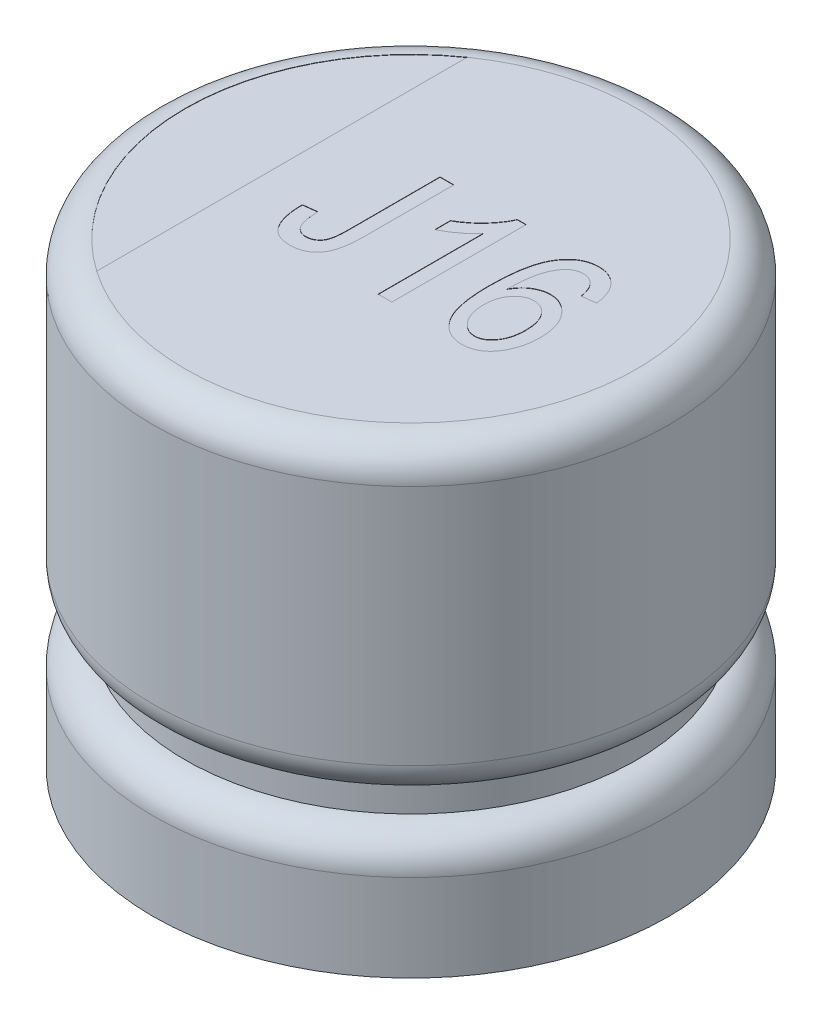
SolidWorks part; units mm, degrees
material "1060-H16"
ref_plane "Front Plane" through (0, 0, 0) normal (0, 0, 1) x (1, 0, 0)
ref_plane "Top Plane" through (0, 0, 0) normal (0, 1, 0) x (1, 0, 0)
ref_plane "Right Plane" through (0, 0, 0) normal (1, 0, 0) x (0, 0, -1)
sketch "Sketch1" plane through (0, 0, 0) normal (0, 1, 0) x (1, 0, 0)
  circle A0 centre (0, 0) radius 8
  dimension "D1" = 16
extrude "Boss-Extrude1" add sketch "Sketch1" along normal blind 14.2
fillet "Fillet1" radius 1 1 edges at (0, 14.2, 8)
sketch "Sketch2" plane through (0, 0, 0) normal (0, 0, 1) x (1, 0, 0)
  line L0 (-8, 13.2) -> (-8, 0) construction
  line L1 (-8, 5.7) -> (-7, 5.7) construction
  line L2 (-8, 5.7) -> (-8, 2.7)
  line L3 (-8, 2.7) -> (-7, 2.7) construction
  line L4 (-7, 5.7) -> (-7, 2.7) construction
  line L5 (7, 14.2) -> (-7, 14.2) construction
  line L6 (-7, 4.7) -> (-7, 3.7)
  arc A0 (-8, 5.7) -> (-7, 4.7) centre (-7, 5.7) ccw
  arc A1 (-7, 3.7) -> (-8, 2.7) centre (-7, 2.7) ccw
  point P8 (-8, 4.2)
  dimension "D1" = 1
  dimension "D2" = 10
  dimension "D3" = 3
ref_axis "Axis1" through (0, -0.75, 0) along (0, 1, 0)
revolve "Cut-Revolve1" cut sketch "Sketch2" angle 360 about axis through (0, -0.75, 0) along (0, 1, 0)
sketch "Sketch3" plane through (0, 14.2, 0) normal (0, 1, 0) x (1, 0, 0)
  line L0 (-4, 5.7446) -> (-4, -5.7446)
  line L1 (0, -55) -> (0, 55) construction
  arc A0 (-4, 5.7446) -> (-4, -5.7446) centre (0, 0) ccw
  circle A1 centre (0, 0) radius 7 construction
  dimension "D1" = 4
extrude "Cut-Extrude1" cut sketch "Sketch3" against normal blind 0.01
sketch "Sketch4" plane through (0, 14.2, 0) normal (0, 1, 0) x (1, 0, 0)
  line L0 (-2.7025, -2) -> (2.7025, -2) construction
  line L1 (0, -55) -> (0, 55) construction
  line L2 (-55, 0) -> (55, 0) construction
  text T0 "J16\r\n" font "Arial Narrow" height in points 16
  point P2 (0, -2)
  dimension "D1" = 2
extrude "Cut-Extrude2" cut sketch "Sketch4" against normal blind 0.01
